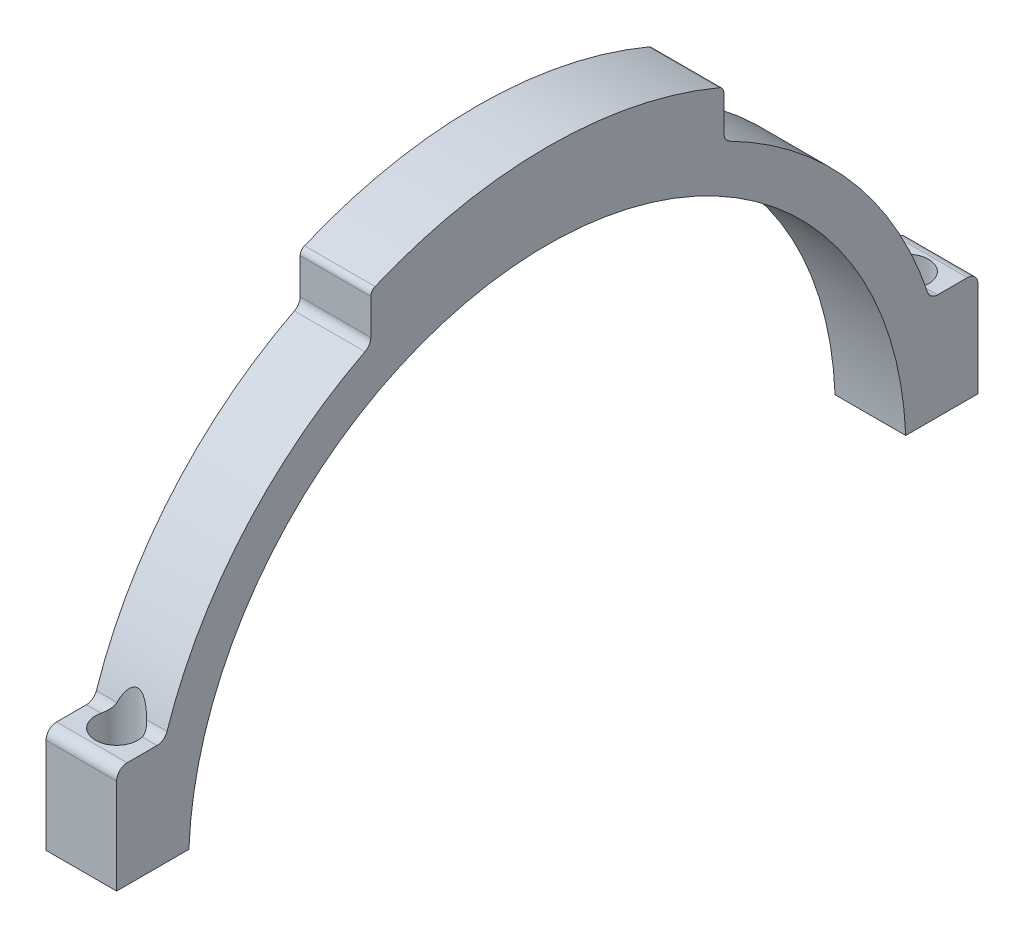
SolidWorks part; units mm, degrees
material "Plain Carbon Steel"
ref_plane "Front Plane" through (0, 0, 0) normal (0, 0, 1) x (1, 0, 0)
ref_plane "Top Plane" through (0, 0, 0) normal (0, 1, 0) x (1, 0, 0)
ref_plane "Right Plane" through (0, 0, 0) normal (1, 0, 0) x (0, 0, -1)
sketch "Sketch1" plane through (0, 0, 0) normal (1, 0, 0) x (0, 0, -1)
  line L0 (0, 56.8) -> (0, 64.8)
  line L2 (-61, 2.0155) -> (-50.76, 2.0155)
  line L3 (50.76, 2.0155) -> (61, 2.0155)
  line L4 (-61, 2.0155) -> (-61, 15.5155)
  line L5 (-59.5, 17.0155) -> (-55.2817, 17.0155)
  line L6 (61, 2.0155) -> (61, 15.5155)
  line L7 (59.5, 17.0155) -> (55.2817, 17.0155)
  line L8 (25, 58.7762) -> (25, 51.9292)
  line L9 (-25, 58.7762) -> (-25, 51.9292)
  arc A0 (50.76, 2.0155) -> (-50.76, 2.0155) centre (0, 0) ccw
  arc A1 (53.8593, 18.0392) -> (25.8182, 50.5931) centre (0, 0) ccw
  circle A2 centre (0, 0) radius 56.8 construction
  circle A3 centre (0, 0) radius 50.8 construction
  arc A4 (-61, 15.5155) -> (-59.5, 17.0155) centre (-59.5, 15.5155) cw
  arc A5 (-55.2817, 17.0155) -> (-53.8593, 18.0392) centre (-55.2817, 18.5155) ccw
  arc A6 (55.2817, 17.0155) -> (53.8593, 18.0392) centre (55.2817, 18.5155) cw
  arc A7 (61, 15.5155) -> (59.5, 17.0155) centre (59.5, 15.5155) ccw
  arc A8 (24.0569, 60.169) -> (-24.0569, 60.169) centre (0, 0) ccw
  arc A9 (61.4452, 20.5799) -> (-61.4452, 20.5799) centre (0, 0) ccw construction
  arc A10 (-25.8182, 50.5931) -> (-53.8593, 18.0392) centre (0, 0) ccw
  arc A11 (53.8593, 18.0392) -> (-53.8593, 18.0392) centre (0, 0) ccw construction
  arc A12 (-25, 51.9292) -> (-25.8182, 50.5931) centre (-26.5, 51.9292) cw
  arc A13 (-24.0569, 60.169) -> (-25, 58.7762) centre (-23.5, 58.7762) ccw
  arc A14 (24.0569, 60.169) -> (25, 58.7762) centre (23.5, 58.7762) cw
  arc A15 (25, 51.9292) -> (25.8182, 50.5931) centre (26.5, 51.9292) ccw
  arc A16 (25, 57.6094) -> (-25, 57.6094) centre (0, 0) ccw
  arc A17 (23.3144, 58.3119) -> (-23.3144, 58.3119) centre (0, 0) ccw construction
  point P32 (-25, 51.0024)
  point P39 (25, 51.0024)
  dimension "D1" = 101.6
  dimension "D2" = 1.5
  dimension "D7" = 1.5
  dimension "D3" = 8
  dimension "D6" = 25
  dimension "D9" = 122
  dimension "D10" = 10.24
  dimension "D11" = 10.24
  dimension "D12" = 15
  dimension "D13" = 15
  dimension "D4" = 8
  dimension "D5" = 6
  dimension "D8" = 2
extrude "Boss-Extrude1" add sketch "Sketch1" along normal blind 10
hole_wizard "M4 Clearance Hole1" positions "Sketch5" profile "Sketch4" hole size "M4" standard "ISO"
sketch "Sketch5" plane through (0, 17.0155, 0) normal (0, 1, 0) x (1, 0, 0)
  line L3 (10, -61) -> (0, -61) construction
  line L4 (0, -61) -> (0, -50.76) construction
  line L5 (10, 50.76) -> (10, 61) construction
  line L6 (10, 61) -> (0, 61) construction
  point P0 (5, 56)
  point P11 (5, -56)
  dimension "D1" = 5
  dimension "D2" = 5
  dimension "D3" = 5
  dimension "D4" = 5
sketch "Sketch4" plane through (5, 17.0155, -56) normal (1, 0, 0) x (0, 0, 1)
  line L0 (0, 0) -> (0, 16.3519)
  line L1 (0, 16.3519) -> (2.25, 15)
  line L2 (2.25, 15) -> (2.25, 0)
  line L5 (2.25, 0) -> (0, 0)
  line L10 (0, 16.3519) -> (-2.25, 15) construction
  line L11 (0, -6.35) -> (0, 107.95) construction
  dimension "Hole Dia." = 4.5
  dimension "Hole Depth" = 15
  dimension "Drill Angle" = 118
sketch "Sketch6" plane through (0, 17.0155, 0) normal (0, 1, 0) x (1, 0, 0)
  circle A0 centre (5, 56) radius 3
  circle A1 centre (5, -56) radius 3
  dimension "D1" = 6
  dimension "D2" = 6
extrude "Cut-Extrude1" cut sketch "Sketch6" along normal blind 8 and the other way blind 6
fillet "Fillet1" radius 1 2 edges at (5, 57.6094, -25) (5, 57.6094, 25)
